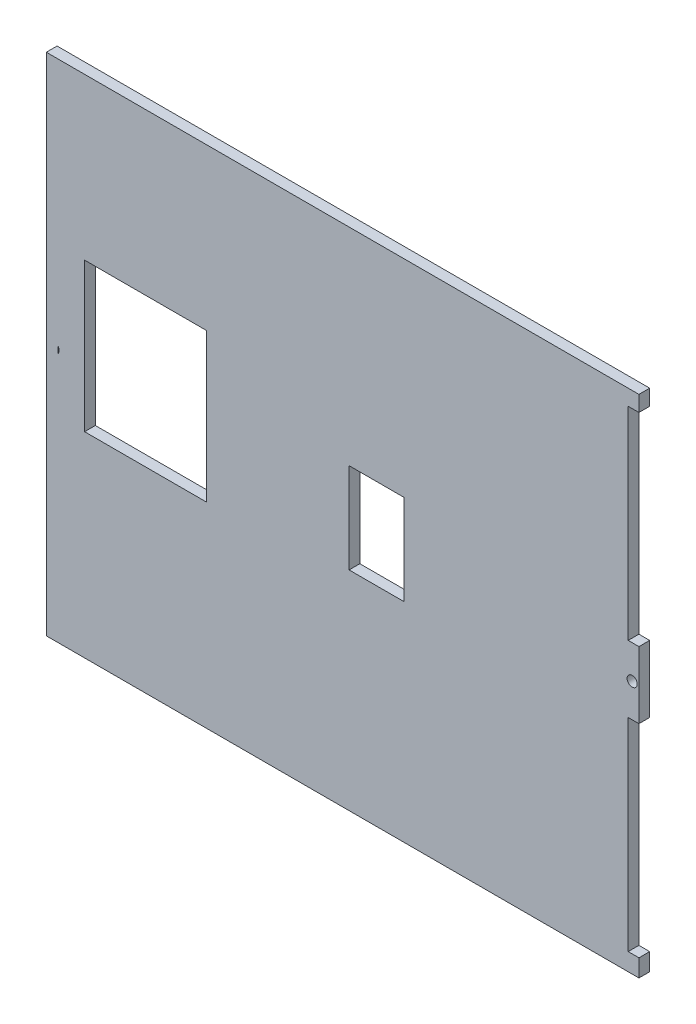
SolidWorks part; units mm, degrees
ref_plane "Front Plane" through (0, 0, 0) normal (0, 0, 1) x (1, 0, 0)
ref_plane "Top Plane" through (0, 0, 0) normal (0, 1, 0) x (1, 0, 0)
ref_plane "Right Plane" through (0, 0, 0) normal (1, 0, 0) x (0, 0, -1)
sketch "Sketch1" plane through (0, 0, 0) normal (0, 0, 1) x (1, 0, 0)
  line L1 (-87.5, 69.85) -> (87.5, 69.85)
  line L2 (-87.5, 69.85) -> (-87.5, -69.85)
  line L3 (-87.5, -69.85) -> (87.5, -69.85)
  line L4 (87.5, 69.85) -> (87.5, -69.85)
  line L5 (-87.5, 69.85) -> (87.5, -69.85) construction
  line L6 (-87.5, -69.85) -> (87.5, 69.85) construction
  point P0 (0, 0)
  dimension "D1" = 139.7
  dimension "D2" = 175
extrude "Boss-Extrude1" add sketch "Sketch1" along normal blind 3.18
sketch "Sketch2" plane through (0, 0, 3.18) normal (0, 0, 1) x (1, 0, 0)
  line L0 (0, 0) -> (87.5, 0) construction
  line L1 (-10, 69.85) -> (10, 69.85)
  line L2 (-10, 69.85) -> (-10, 66.67)
  line L3 (-10, 66.67) -> (-1.5, 66.67)
  line L4 (10, 69.85) -> (10, 66.67)
  line L5 (87.5, -69.85) -> (87.5, 69.85) construction
  line L6 (0, 0) -> (0, 69.85) construction
  line L7 (-1.5, 56.67) -> (1.5, 56.67)
  line L8 (-1.5, 56.67) -> (-1.5, 59.67)
  line L10 (1.5, 56.67) -> (1.5, 59.67)
  line L12 (87.5, 69.85) -> (-87.5, 69.85) construction
  line L13 (3.5, 62.67) -> (1.5, 62.67)
  line L14 (3.5, 62.67) -> (3.5, 59.67)
  line L15 (3.5, 59.67) -> (1.5, 59.67)
  line L16 (-3.5, 62.67) -> (-3.5, 59.67)
  line L17 (-10, -69.85) -> (-10, -66.67)
  line L18 (-10, -66.67) -> (-1.5, -66.67)
  line L19 (-1.5, -62.67) -> (-1.5, -66.67)
  line L20 (-1.5, -62.67) -> (-3.5, -62.67)
  line L21 (-3.5, -62.67) -> (-3.5, -59.67)
  line L22 (1.5, 66.67) -> (10, 66.67)
  line L23 (-1.5, 62.67) -> (-3.5, 62.67)
  line L24 (-1.5, -59.67) -> (-3.5, -59.67)
  line L25 (-1.5, -56.67) -> (-1.5, -59.67)
  line L26 (-1.5, -56.67) -> (1.5, -56.67)
  line L27 (-1.5, 59.67) -> (-3.5, 59.67)
  line L28 (1.5, -56.67) -> (1.5, -59.67)
  line L29 (-1.5, 62.67) -> (-1.5, 66.67)
  line L30 (1.5, 62.67) -> (1.5, 66.67)
  line L31 (3.5, -59.67) -> (1.5, -59.67)
  line L32 (3.5, -62.67) -> (3.5, -59.67)
  line L33 (3.5, -62.67) -> (1.5, -62.67)
  line L34 (1.5, -62.67) -> (1.5, -66.67)
  line L35 (1.5, -66.67) -> (10, -66.67)
  line L36 (10, -69.85) -> (10, -66.67)
  line L37 (-10, -69.85) -> (10, -69.85)
  line L38 (-87.5, 69.85) -> (-87.5, -69.85) construction
  line L39 (-87.5, 69.85) -> (-84.32, 69.85)
  line L40 (-87.5, 69.85) -> (-87.5, 9.875)
  line L41 (-87.5, 9.875) -> (-84.32, 9.875)
  line L42 (-84.32, 69.85) -> (-84.32, 9.875)
  line L43 (-87.5, -69.85) -> (-84.32, -69.85)
  line L44 (-87.5, -69.85) -> (-87.5, -9.875)
  line L45 (-87.5, -9.875) -> (-84.32, -9.875)
  line L46 (-84.32, -69.85) -> (-84.32, -9.875)
  line L47 (87.5, -9.875) -> (84.32, -9.875)
  line L48 (84.32, -69.85) -> (84.32, -9.875)
  line L49 (87.5, -69.85) -> (84.32, -69.85)
  line L50 (87.5, -69.85) -> (87.5, -9.875)
  line L51 (87.5, 9.875) -> (84.32, 9.875)
  line L52 (84.32, 69.85) -> (84.32, 9.875)
  line L53 (87.5, 69.85) -> (84.32, 69.85)
  line L54 (87.5, 69.85) -> (87.5, 9.875)
  line L70 (-28.8549, -66.67) -> (-20.3341, -66.67)
  line L71 (-40.3341, -69.85) -> (-20.3341, -69.85)
  line L72 (-40.3341, -69.85) -> (-40.3341, -66.67)
  line L73 (-40.3341, -66.67) -> (-31.8549, -66.67)
  line L74 (-20.3341, -69.85) -> (-20.3341, -66.67)
  line L75 (-31.8549, -62.67) -> (-33.773, -62.67)
  line L76 (-87.5, -69.85) -> (87.5, -69.85) construction
  line L77 (-31.8549, -56.85) -> (-28.8549, -56.85)
  line L78 (-31.8549, -56.85) -> (-31.8549, -59.67)
  line L80 (-28.8549, -56.85) -> (-28.8549, -59.67)
  line L83 (-26.773, -62.67) -> (-28.8549, -62.67)
  line L84 (-26.773, -62.67) -> (-26.773, -59.67)
  line L85 (-26.773, -59.67) -> (-28.8549, -59.67)
  line L86 (-33.773, -62.67) -> (-33.773, -59.67)
  line L91 (-31.8549, -59.67) -> (-33.773, -59.67)
  line L98 (-31.8549, -62.67) -> (-31.8549, -66.67)
  line L99 (-28.8549, -62.67) -> (-28.8549, -66.67)
  circle A0 centre (-85.5, 0) radius 1.5
  circle A1 centre (85.5, 0) radius 1.5
  point P0 (0, 50.5662)
  point P5 (0, 32.0079)
  point P10 (15.4931, 34.4893)
  point P67 (-32.11, -66.8097)
  point P72 (-32.3859, -61.3492)
  point P77 (-32.3859, -59.7197)
  dimension "D11" = 3
  dimension "D12" = 2
  dimension "D1" = 20
  dimension "D2" = 19.75
  dimension "D3" = 4
  dimension "D4" = 3
  dimension "D5" = 3.18
  dimension "D6" = 7
  dimension "D7" = 3
  dimension "D8" = 3
  dimension "D9" = 3.18
  dimension "D10" = 3.18
  dimension "D13" = 20
  dimension "D14" = 7
  dimension "D15" = 3.18
  dimension "D16" = 3
  dimension "D17" = 3
  dimension "D18" = 4
  dimension "D19" = 13
extrude "Cut-Extrude1" cut sketch "Sketch2" against normal through all
sketch "Sketch3" plane through (0, 0, 0) normal (0, 0, -1) x (-1, 0, 0)
  circle A0 centre (-35.6713, -47.9634) radius 1.59
  circle A1 centre (-35.6713, -30.7773) radius 1.59
extrude "Cut-Extrude2" cut sketch "Sketch3" against normal through all
sketch "Sketch4" plane through (0, 0, 0) normal (0, 0, -1) x (-1, 0, 0)
  circle A0 centre (-34.7507, 53.7803) radius 1.59
  circle A1 centre (-34.7507, 36.5942) radius 1.59
  circle A2 centre (36.2498, 53.7803) radius 1.59
  circle A3 centre (36.2498, 36.5942) radius 1.59
  circle A4 centre (35.9839, -30.7773) radius 1.59
  circle A5 centre (35.9839, -47.9634) radius 1.59
  circle A6 centre (-35.6713, -30.7773) radius 1.59
  circle A7 centre (-35.6713, -47.9634) radius 1.59
extrude "Cut-Extrude3" cut sketch "Sketch4" against normal through all
sketch "Sketch5" plane through (0, 0, 3.18) normal (0, 0, 1) x (1, 0, 0)
  line L1 (-46.5267, 67.382) -> (45.3995, 67.382)
  line L2 (-46.5267, 67.382) -> (-46.5267, -56.2746)
  line L3 (-46.5267, -56.2746) -> (45.3995, -56.2746)
  line L4 (45.3995, 67.382) -> (45.3995, -56.2746)
extrude "Boss-Extrude2" add sketch "Sketch5" against normal blind 3.18
sketch "Sketch6" plane through (0, 0, 0) normal (0, 0, -1) x (-1, 0, 0)
  line L1 (-26.8, -9.839) -> (-23.62, -9.839)
  line L2 (-26.8, -9.839) -> (-26.8, 9.911)
  line L3 (-26.8, 9.911) -> (-23.62, 9.911)
  line L4 (-23.62, -9.839) -> (-23.62, 9.911)
  line L5 (11.4836, -9.875) -> (14.6636, -9.875)
  line L6 (11.4836, -9.875) -> (11.4836, 9.875)
  line L7 (11.4836, 9.875) -> (14.6636, 9.875)
  line L8 (14.6636, -9.875) -> (14.6636, 9.875)
extrude "Cut-Extrude4" cut sketch "Sketch6" against normal through all
sketch "Sketch8" plane through (0, 0, 0) normal (0, 0, -1) x (-1, 0, 0)
  line L1 (10, -69.85) -> (-15.5604, -69.85)
  line L2 (10, -69.85) -> (10, -50.1707)
  line L3 (10, -50.1707) -> (-15.5604, -50.1707)
  line L4 (-15.5604, -69.85) -> (-15.5604, -50.1707)
extrude "Boss-Extrude3" add sketch "Sketch8" against normal blind 3.18
sketch "Sketch10" plane through (0, 0, 0) normal (0, 0, -1) x (-1, 0, 0)
  line L1 (-10, 67.382) -> (10, 67.382)
  line L2 (-10, 67.382) -> (-10, 69.85)
  line L3 (-10, 69.85) -> (10, 69.85)
  line L4 (10, 67.382) -> (10, 69.85)
extrude "Boss-Extrude4" add sketch "Sketch10" against normal blind 3.18
sketch "Sketch11" plane through (0, 0, 0) normal (0, 0, -1) x (-1, 0, 0)
  line L0 (-84.32, 69.85) -> (84.32, 69.85) construction
  line L1 (20.7931, 66.67) -> (29.4791, 66.67)
  line L2 (20.7931, 66.67) -> (20.7931, 69.85)
  line L3 (20.7931, 69.85) -> (40.7931, 69.85)
  line L4 (40.7931, 66.67) -> (40.7931, 69.85)
  line L6 (30.7931, 0) -> (0, 0) construction
  line L7 (29.4791, 62.67) -> (29.4791, 66.67)
  line L8 (29.4791, 56.85) -> (32.4791, 56.85)
  line L9 (29.4791, 56.85) -> (29.4791, 59.67)
  line L11 (32.4791, 56.85) -> (32.4791, 59.67)
  line L12 (32.4791, 66.67) -> (40.7931, 66.67)
  line L14 (27.2931, 59.67) -> (29.4791, 59.67)
  line L15 (27.2931, 59.67) -> (27.2931, 62.67)
  line L16 (27.2931, 62.67) -> (29.4791, 62.67)
  line L17 (34.2931, 59.67) -> (34.2931, 62.67)
  line L22 (30.7931, 56.85) -> (30.7931, 0) construction
  line L25 (32.4791, 62.67) -> (32.4791, 66.67)
  line L26 (32.4791, 59.67) -> (34.2931, 59.67)
  line L28 (32.4791, 62.67) -> (34.2931, 62.67)
  point P8 (30.4223, 62.891)
  point P11 (30.7931, 69.85)
  point P15 (30.4223, 62.1751)
  dimension "D1" = 20
  dimension "D2" = 3
  dimension "D3" = 3
  dimension "D4" = 13
  dimension "D5" = 7
  dimension "D6" = 4
extrude "Cut-Extrude5" cut sketch "Sketch11" against normal through all
sketch "Sketch12" plane through (0, 0, 0) normal (0, 0, -1) x (-1, 0, 0)
  line L1 (40.471, -17.0656) -> (76.4831, -17.0656)
  line L2 (40.471, -17.0656) -> (40.471, 26.8946)
  line L3 (40.471, 26.8946) -> (76.4831, 26.8946)
  line L4 (76.4831, -17.0656) -> (76.4831, 26.8946)
  line L5 (40.471, -17.0656) -> (76.4831, 26.8946) construction
  line L6 (40.471, 26.8946) -> (76.4831, -17.0656) construction
  point P0 (58.477, 4.9145)
extrude "Cut-Extrude6" cut sketch "Sketch12" against normal through all
sketch "Sketch13" plane through (0, 0, 0) normal (0, 0, -1) x (-1, 0, 0)
  line L1 (-17.9359, -13.3526) -> (-1.7618, -13.3526)
  line L2 (-17.9359, -13.3526) -> (-17.9359, 13.3526)
  line L3 (-17.9359, 13.3526) -> (-1.7618, 13.3526)
  line L4 (-1.7618, -13.3526) -> (-1.7618, 13.3526)
  line L5 (-17.9359, -13.3526) -> (-1.7618, 13.3526) construction
  line L6 (-17.9359, 13.3526) -> (-1.7618, -13.3526) construction
  point P0 (-9.8488, 0)
extrude "Cut-Extrude7" cut sketch "Sketch13" against normal through all
sketch "Sketch14" plane through (84.32, 0, 0) normal (1, 0, 0) x (0, 0, -1)
  line L1 (0, -69.85) -> (-3.18, -69.85)
  line L2 (0, -69.85) -> (0, 69.85)
  line L3 (0, 69.85) -> (-3.18, 69.85)
  line L4 (-3.18, -69.85) -> (-3.18, 69.85)
sketch "Sketch16" plane through (0, 0, 0) normal (0, 0, -1) x (-1, 0, 0)
  line L0 (20.3341, -69.85) -> (-84.32, -69.85) construction
  line L1 (-41.3018, -69.85) -> (-22.4174, -69.85)
  line L2 (-41.3018, -69.85) -> (-41.3018, 51.2062)
  line L3 (-41.3018, 51.2062) -> (-22.4174, 51.2062)
  line L4 (-22.4174, -69.85) -> (-22.4174, 51.2062)
  line L6 (6.6847, 15.8036) -> (17.5418, 15.8036)
  line L7 (6.6847, 15.8036) -> (6.6847, -19.634)
  line L8 (6.6847, -19.634) -> (17.5418, -19.634)
  line L9 (17.5418, 15.8036) -> (17.5418, -19.634)
  line L10 (17.5418, -69.85) -> (45.9706, -69.85)
  line L11 (17.5418, -69.85) -> (17.5418, -55.8486)
  line L12 (17.5418, -55.8486) -> (45.9706, -55.8486)
  line L13 (45.9706, -69.85) -> (45.9706, -55.8486)
  line L14 (20.7931, 69.85) -> (43.3701, 69.85)
  line L15 (20.7931, 69.85) -> (20.7931, 53.1205)
  line L16 (20.7931, 53.1205) -> (43.3701, 53.1205)
  line L17 (43.3701, 69.85) -> (43.3701, 53.1205)
extrude "Boss-Extrude6" add sketch "Sketch16" against normal blind 3.18
sketch "Sketch17" plane through (0, 0, 0) normal (0, 0, -1) x (-1, 0, 0)
  line L1 (-87.5, -69.85) -> (84.32, -69.85)
  line L2 (-87.5, -69.85) -> (-87.5, -75.025)
  line L3 (-87.5, -75.025) -> (84.32, -75.025)
  line L5 (84.32, 69.85) -> (-87.5, 69.85)
  line L7 (84.32, 74.4938) -> (-87.5, 74.4938)
  line L8 (-87.5, 69.85) -> (-87.5, 74.4938)
  line L10 (84.32, -69.85) -> (84.32, 69.85)
  line L11 (84.32, 74.4938) -> (87.8082, 74.4938)
  line L12 (87.8082, -69.85) -> (87.8082, 74.4938)
  line L13 (84.32, -75.025) -> (87.8082, -75.025)
  line L16 (87.8082, -75.025) -> (87.8082, -69.85)
extrude "Boss-Extrude7" add sketch "Sketch17" against normal blind 3.18
sketch "Sketch18" plane through (0, 0, 3.18) normal (0, 0, 1) x (1, 0, 0)
  line L0 (-87.8082, -75.025) -> (-87.8082, 74.4938) construction
  line L1 (87.5, -75.025) -> (-87.8082, -75.025)
  line L2 (87.5, -75.025) -> (87.5, -65.2062)
  line L3 (87.5, -65.2062) -> (-87.8082, -65.2062)
  line L4 (-87.8082, -75.025) -> (-87.8082, -65.2062)
